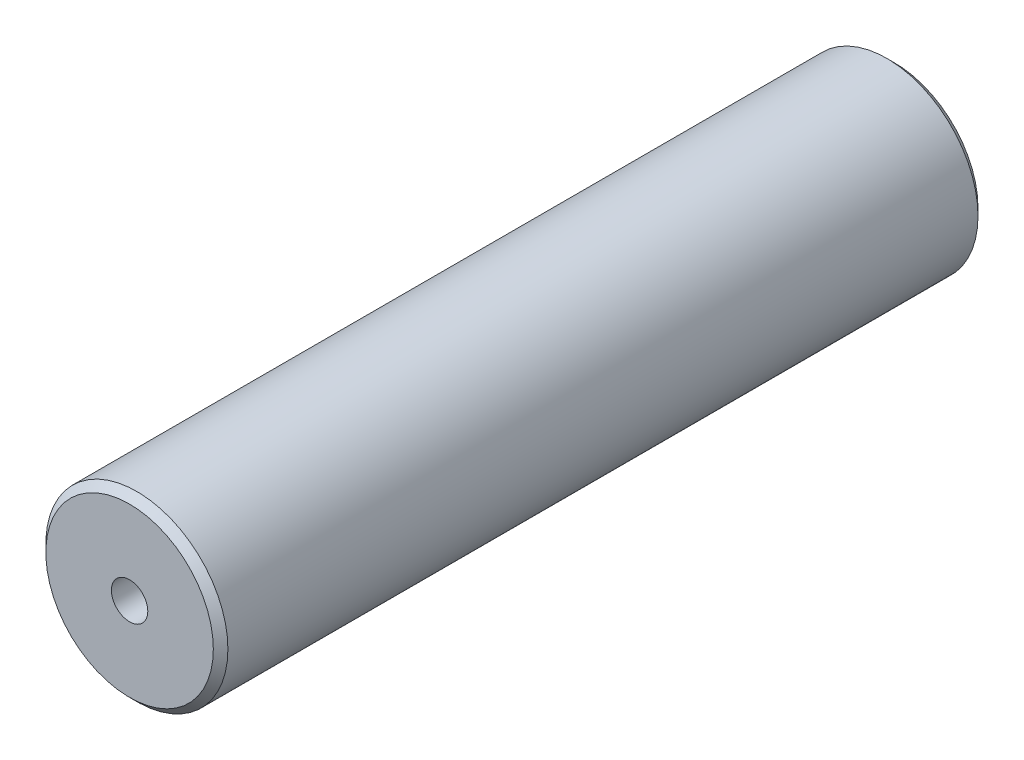
SolidWorks part; units mm, degrees
ref_plane "Front Plane" through (0, 0, 0) normal (0, 0, 1) x (1, 0, 0)
ref_plane "Top Plane" through (0, 0, 0) normal (0, 1, 0) x (1, 0, 0)
ref_plane "Right Plane" through (0, 0, 0) normal (1, 0, 0) x (0, 0, -1)
sketch "Sketch1" plane through (0, 0, 0) normal (0, 0, 1) x (1, 0, 0)
  circle A0 centre (0, 0) radius 12.5
  dimension "D1" = 25
extrude "Boss-Extrude1" add sketch "Sketch1" along normal mid plane 105
chamfer "Chamfer1" distance 1 angle 45 2 edges at (12.5, 0, -52.5) (12.5, 0, 52.5)
hole_wizard "Tap Drill for M6 Tap1" positions "Sketch2" profile "Sketch4" hole size "M6" standard "ISO"
sketch "Sketch2" plane through (0, 0, 52.5) normal (0, 0, 1) x (1, 0, 0)
  point P0 (0, 0)
sketch "Sketch4" plane through (0, 0, 52.5) normal (1, 0, 0) x (0, -1, 0)
  line L0 (0, 0) -> (0, 14.5022)
  line L1 (0, 14.5022) -> (2.5, 13)
  line L2 (2.5, 13) -> (2.5, 0)
  line L5 (2.5, 0) -> (0, 0)
  line L10 (0, 14.5022) -> (-2.5, 13) construction
  line L11 (0, -6.35) -> (0, 107.95) construction
  dimension "Hole Dia." = 5
  dimension "Hole Depth" = 13
  dimension "Drill Angle" = 118
mirror "Mirror1" about plane through (0, 0, 0) normal (0, 0, 1) of "Tap Drill for M6 Tap1"
